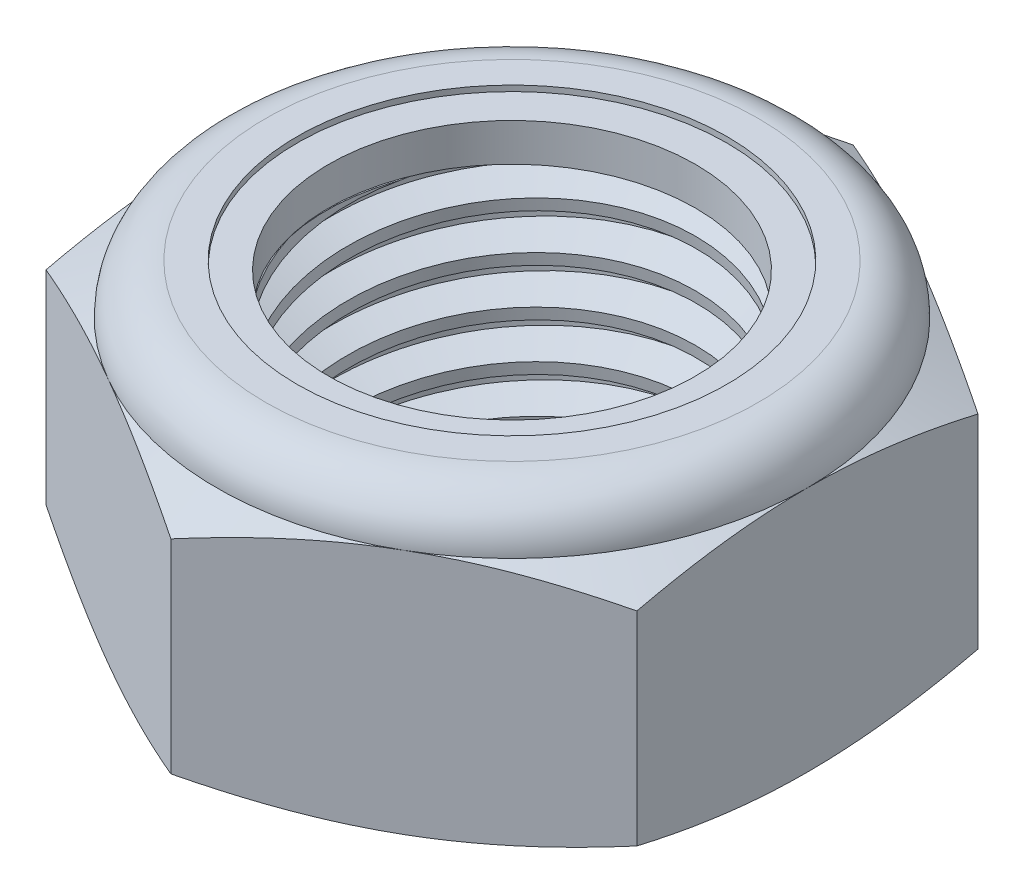
SolidWorks part; units mm, degrees
ref_plane "Front" through (0, 0, 0) normal (0, 0, 1) x (1, 0, 0)
ref_plane "Top" through (0, 0, 0) normal (0, 1, 0) x (1, 0, 0)
ref_plane "Right" through (0, 0, 0) normal (1, 0, 0) x (0, 0, -1)
sketch "Sketch1" plane through (0, 0, 0) normal (0, 1, 0) x (1, 0, 0)
  line L1 (0, 9.1654) -> (-7.9375, 4.5827)
  line L2 (-7.9375, 4.5827) -> (-7.9375, -4.5827)
  line L3 (-7.9375, -4.5827) -> (0, -9.1654)
  line L4 (0, -9.1654) -> (7.9375, -4.5827)
  line L5 (7.9375, -4.5827) -> (7.9375, 4.5827)
  line L6 (7.9375, 4.5827) -> (0, 9.1654)
  circle A0 centre (0, 0) radius 7.9375 construction
  dimension "Hex Flats" = 15.875
extrude "Extrude1" add sketch "Sketch1" along normal blind 7.9375
sketch "Sketch2" plane through (0, 0, 0) normal (1, 0, 0) x (0, 0, -1)
  line L0 (-5.5499, 0) -> (-5.5499, 7.9375) construction
  line L1 (0, 0) -> (5.5499, 0)
  line L2 (0, 0) -> (0, 7.9375)
  line L3 (0, 7.9375) -> (5.5499, 7.9375)
  line L4 (5.5499, 0) -> (5.5499, 7.9375)
  line L5 (-4.5827, 7.9375) -> (4.5827, 7.9375) construction
  line L7 (0, -5.5499) -> (0, 0) construction
  dimension "Thread Dia" = 11.0998
revolve "Revolve1" add sketch "Sketch2" angle 360 about L7
sketch "Sketch3" plane through (0, 0, 0) normal (1, 0, 0) x (0, 0, -1)
  line L0 (5.5499, 7.9375) -> (-5.5499, 7.9375) construction
  line L1 (-5.5499, 7.9375) -> (-5.5499, 6.6675) construction
  line L2 (-5.5499, 6.6675) -> (5.5499, 7.9375) construction
  line L3 (5.5499, 7.9375) -> (5.5679, 7.7798) construction
  line L4 (5.5679, 7.7798) -> (5.6943, 6.6757)
  line L5 (5.6943, 6.6757) -> (4.9662, 6.9919)
  line L6 (4.9662, 6.9919) -> (4.9301, 7.3073)
  line L7 (4.9301, 7.3073) -> (5.5679, 7.7798)
  line L8 (4.9482, 7.1496) -> (5.6311, 7.2278) construction
  line L9 (5.5499, 7.9375) -> (5.5499, 7.2185) construction
  line L10 (5.5499, 7.2185) -> (-5.5499, 5.9485) construction
  line L11 (-5.5499, 5.9485) -> (-5.5499, 6.6675) construction
  line L12 (-0.1549, 7.9375) -> (0.1549, 5.2294) construction
  line L13 (-5.5499, 0) -> (-5.5499, 7.9375) construction
  line L14 (0, 7.9375) -> (5.5499, 7.9375) construction
  line L15 (5.5499, 0) -> (5.5499, 7.9375) construction
  point P13 (0, 6.5835)
  dimension "D1" = 0.1588
  dimension "D2" = 0.3175
  dimension "Thread Pitch" = 1.27
  dimension "D4" = 60
  dimension "D5" = 1.27
revolve "Cut-Revolve1" cut sketch "Sketch3" angle 360 about L12
pattern_linear "LPattern1" count 6 spacing 1.27 along (0, -1, 0) count 2 spacing 1.27 along (0, 1, 0) of "Cut-Revolve1"
sketch "Sketch4" plane through (0, 0, 0) normal (1, 0, 0) x (0, 0, -1)
  line L0 (0, 7.9375) -> (5.5499, 7.9375)
  line L1 (5.5499, 7.9375) -> (4.9301, 7.6485)
  line L2 (4.9301, 7.6485) -> (4.9301, 0.289)
  line L3 (4.9301, 0.289) -> (5.5499, 0)
  line L4 (5.5499, 0) -> (0, 0)
  line L5 (0, 0) -> (0, 7.9375)
  line L6 (5.5499, 0) -> (5.5499, 7.9375) construction
  line L7 (0, 7.9375) -> (5.5499, 7.9375) construction
  line L8 (0, 0) -> (5.5499, 0) construction
  line L9 (0, 0) -> (0, 7.9375) construction
  line L10 (0, 7.9375) -> (0, 8.6214) construction
  dimension "D1" = 25
revolve "Cut-Revolve2" cut sketch "Sketch4" angle 360 about L10
combine bodies "Combine1" operation type subtract main body 112 bodies to subtract 111
sketch "Sketch5" plane through (0, 0, 0) normal (1, 0, 0) x (0, 0, -1)
  line L0 (0, 0) -> (7.9375, 0)
  line L1 (7.9375, 0) -> (9.1654, 0.5726)
  line L2 (9.1654, 0.5726) -> (9.1654, 6.042)
  line L3 (9.1654, 6.042) -> (7.9375, 6.6146)
  line L4 (6.6146, 7.9375) -> (6.6146, 9.2075)
  line L5 (6.6146, 9.2075) -> (10.4354, 9.2075)
  line L6 (10.4354, 9.2075) -> (10.4354, -1.27)
  line L7 (10.4354, -1.27) -> (0, -1.27)
  line L8 (0, -1.27) -> (0, 0)
  line L9 (7.9375, 6.6146) -> (7.9375, 0) construction
  line L10 (0, 0) -> (5.5499, 0) construction
  line L13 (9.1654, 3.3073) -> (10.4354, 3.3073) construction
  line L14 (9.1654, 7.9375) -> (9.1654, 0) construction
  line L15 (0, 0) -> (0, 9.2075) construction
  line L20 (0, 9.2075) -> (6.6146, 9.2075) construction
  line L22 (0, 7.9375) -> (5.5499, 7.9375) construction
  arc A0 (7.9375, 6.6146) -> (6.6146, 7.9375) centre (6.6146, 6.6146) ccw
  dimension "D1" = 25
  dimension "D2" = 1.27
  dimension "D3" = 7.9375
  dimension "D4" = 1.3229
revolve "Cut-Revolve3" cut sketch "Sketch5" angle 360 about L15
sketch "Sketch6" plane through (0, 0, 0) normal (1, 0, 0) x (0, 0, -1)
  line L0 (0, 6.6146) -> (7.7851, 6.6146)
  line L1 (6.6146, 7.7851) -> (5.7723, 7.7851)
  line L2 (0, 9.2075) -> (0, 6.6146)
  line L3 (5.7723, 9.2075) -> (0, 9.2075)
  line L4 (0, 9.2075) -> (6.6146, 9.2075) construction
  line L5 (0, 0) -> (0, 9.2075) construction
  line L6 (0, 9.2075) -> (0, 44.323) construction
  line L7 (5.7723, 7.7851) -> (5.7723, 9.2075)
  line L8 (6.6146, 7.9375) -> (6.6146, 7.7851) construction
  line L9 (5.7723, 7.7851) -> (4.9301, 7.7851) construction
  line L10 (4.9301, 7.7851) -> (4.9301, 7.6485) construction
  arc A0 (7.7851, 6.6146) -> (6.6146, 7.7851) centre (6.6146, 6.6146) ccw
  arc A1 (7.9375, 6.6146) -> (6.6146, 7.9375) centre (6.6146, 6.6146) ccw construction
  dimension "D1" = 0.1524
revolve "Cut-Revolve4" cut sketch "Sketch6" angle 360 about L6
sketch "Sketch7" plane through (0, 0, 0) normal (1, 0, 0) x (0, 0, -1)
  line L0 (4.9301, 6.6908) -> (7.7062, 6.6908)
  line L1 (6.6146, 7.7089) -> (4.9301, 7.7089)
  line L2 (4.9301, 7.7089) -> (4.9301, 6.6908)
  line L3 (4.9301, 6.6908) -> (0, 6.6908) construction
  line L4 (0, 6.6908) -> (0, 7.7089) construction
  line L5 (0, 7.7089) -> (4.9301, 7.7089) construction
  line L6 (4.9301, 6.6908) -> (4.9301, 6.6146) construction
  line L7 (0, 6.6146) -> (7.7851, 6.6146) construction
  line L8 (6.6146, 7.7089) -> (6.6146, 7.7851) construction
  arc A0 (7.7062, 6.6908) -> (6.6146, 7.7089) centre (6.6146, 6.6146) ccw
  arc A2 (7.7851, 6.6146) -> (6.6146, 7.7851) centre (6.6146, 6.6146) ccw construction
  dimension "D1" = 0.0762
revolve "Revolve2" add sketch "Sketch7" angle 360 about L4
equation "\"D1@Sketch3\"=\"Thread Pitch@Sketch3\"/8"
equation "\"D2@Sketch3\"=\"Thread Pitch@Sketch3\"/4"
equation "\"D5@Sketch3\"=\"Thread Pitch@Sketch3\""
equation "\"D4@LPattern1\"=\"Thread Pitch@Sketch3\""
equation "\"D3@LPattern1\"=\"Thread Pitch@Sketch3\""
equation "\"D1@LPattern1\"=\"Height@Extrude1\"/\"Thread Pitch@Sketch3\""
equation "\"D4@Sketch5\"=\"Height@Extrude1\"/6"
